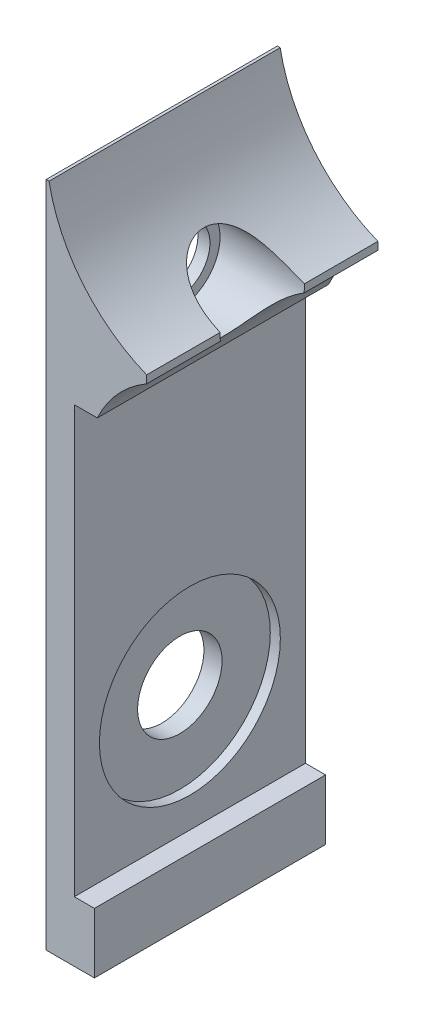
SolidWorks part; units mm, degrees
ref_plane "Alzado" through (0, 0, 0) normal (0, 0, 1) x (1, 0, 0)
ref_plane "Planta" through (0, 0, 0) normal (0, 1, 0) x (1, 0, 0)
ref_plane "Vista lateral" through (0, 0, 0) normal (1, 0, 0) x (0, 0, -1)
sketch "Croquis1" plane through (0, 0, 0) normal (0, 0, 1) x (1, 0, 0)
  line L0 (-89.2534, -13.3365) -> (-89.2534, 19.8635)
  line L1 (-89.2534, 19.8635) -> (-87.8534, 19.8635)
  line L2 (-89.2534, -13.3365) -> (-86.8534, -13.3365)
  line L3 (-86.8534, -13.3365) -> (-86.8534, -10.3365)
  line L4 (-86.8534, -10.3365) -> (-87.8534, -10.3365)
  line L5 (-87.8534, 19.8635) -> (-87.8534, 13.8635) construction
  line L6 (-87.8534, 13.8635) -> (-87.8534, 10.8635) construction
  line L7 (-87.8534, 10.8635) -> (-84.2534, 10.8635)
  line L8 (-84.2534, 10.8635) -> (-84.2534, 16.8635)
  line L9 (-84.2534, 16.8635) -> (-87.8534, 16.8635)
  line L10 (-87.8534, 16.8635) -> (-87.8534, 19.8635)
  line L11 (-87.8534, 10.8635) -> (-87.8534, -10.3365)
  dimension "D1" = 33.2
  dimension "D2" = 1.4
  dimension "D3" = 2.4
  dimension "D4" = 3
  dimension "D5" = 6
  dimension "D6" = 3.6
extrude "Saliente-Extruir1" add sketch "Croquis1" along normal blind 11.5
sketch "Croquis2" plane through (-84.2534, 0, 0) normal (1, 0, 0) x (0, 0, -1)
  line L0 (-11.5, 10.8635) -> (0, 16.8635) construction
  line L1 (-5.75, -13.3365) -> (-5.75, -4.3365) construction
  line L2 (-11.5, -13.3365) -> (0, -13.3365) construction
  circle A0 centre (-5.75, 13.8635) radius 2.1
  circle A1 centre (-5.75, -4.3365) radius 2.1
  dimension "D1" = 9
  dimension "D2" = 4.2
  dimension "D3" = 4.2
extrude "Cortar-Extruir1" cut sketch "Croquis2" against normal up to vertex
sketch "Croquis3" plane through (-87.8534, 0, 0) normal (1, 0, 0) x (0, 0, -1)
  circle A0 centre (-5.75, -4.3365) radius 4.5
  dimension "D1" = 9
extrude "Cortar-Extruir2" cut sketch "Croquis3" against normal blind 0.5
sketch "Croquis4" plane through (-89.2534, 0, 0) normal (-1, 0, 0) x (0, 0, 1)
  circle A0 centre (5.75, 13.8635) radius 3
  dimension "D1" = 6
extrude "Cortar-Extruir3" cut sketch "Croquis4" against normal blind 0.2
sketch "Croquis5" plane through (-89.0534, 0, 0) normal (-1, 0, 0) x (0, 0, 1)
  circle A0 centre (5.75, 13.8635) radius 2.1
  circle A1 centre (5.75, 13.8635) radius 1.6
  dimension "D1" = 0.5
extrude "Saliente-Extruir2" add sketch "Croquis5" against normal blind 0.6
sketch "Croquis6" plane through (0, 0, 11.5) normal (0, 0, 1) x (1, 0, 0)
  line L0 (-89.2534, 13.8635) -> (-81.2534, 13.8635) construction
  line L1 (-89.2534, 19.8635) -> (-89.2534, -13.3365) construction
  line L2 (-81.2534, 13.8635) -> (-81.2534, 8.3635) construction
  line L3 (-81.2534, 13.8635) -> (-81.2534, 21.3635) construction
  arc A4 (-78.6862, 13.7866) -> (-83.8205, 13.7866) centre (-81.2534, 21.3635) ccw
  arc A5 (-78.6862, 13.7866) -> (-83.8205, 13.7866) centre (-81.2534, 8.3635) cw
  dimension "D1" = 8
  dimension "D2" = 7.5
  dimension "D3" = 5.5
extrude "Cortar-Extruir5" cut sketch "Croquis6" against normal up to vertex (11.5 mm away)
